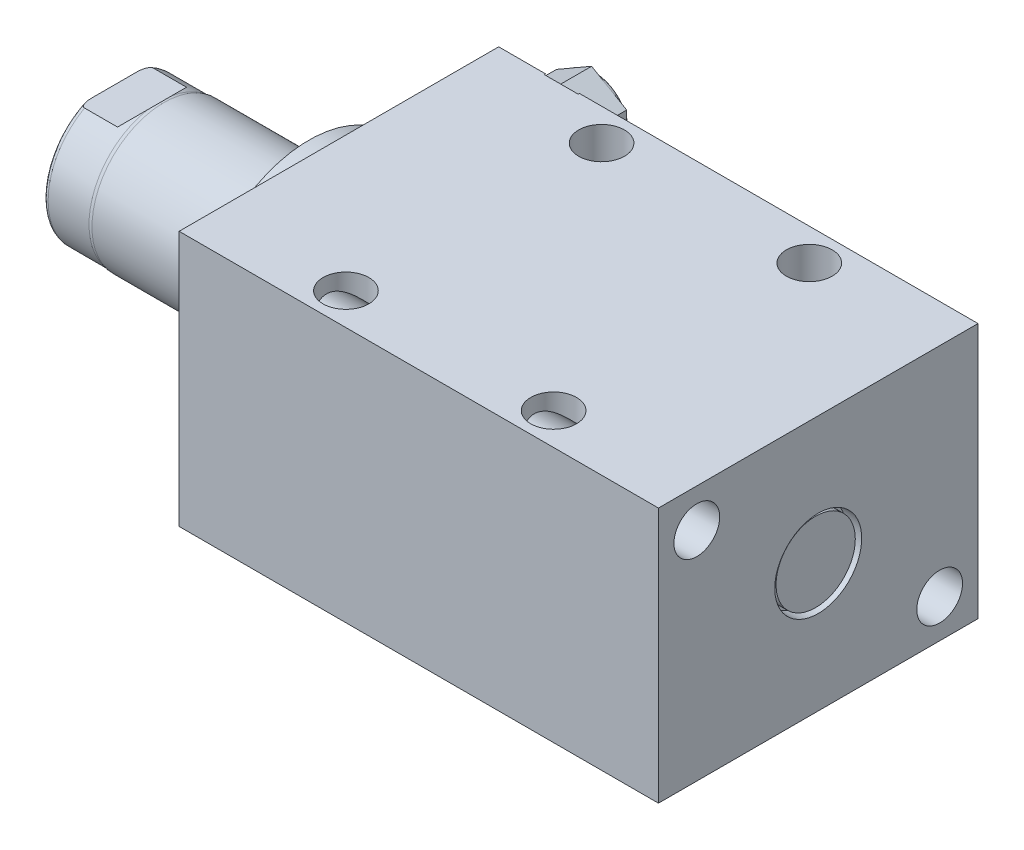
SolidWorks part; units mm, degrees
material "Alloy Steel"
ref_plane "Front Plane" through (0, 0, 0) normal (0, 0, 1) x (1, 0, 0)
ref_plane "Top Plane" through (0, 0, 0) normal (0, 1, 0) x (1, 0, 0)
ref_plane "Right Plane" through (0, 0, 0) normal (1, 0, 0) x (0, 0, -1)
ref_plane "Plane1" through (0, 0, 0) normal (1, 0, 0) x (0, 0, -1)
sketch "Sketch1" plane through (0, 0, 0) normal (1, 0, 0) x (0, 0, -1)
  line L0 (-31.75, 25.4) -> (31.75, 25.4)
  line L1 (31.75, 25.4) -> (31.75, -25.4)
  line L2 (31.75, -25.4) -> (-31.75, -25.4)
  line L3 (-31.75, -25.4) -> (-31.75, 25.4)
  line L4 (0, -24.4475) -> (0, 24.4475) construction
  dimension "D1" = 50.8
  dimension "D2" = 25.4
  dimension "D3" = 63.5
  dimension "D4" = 31.75
extrude "Extrude1" add sketch "Sketch1" along normal blind 95.25
ref_plane "Plane12" through (0, 17.45, 0) normal (0, 1, 0) x (-1, 0, 0)
sketch "S2D0002" plane through (0, 17.45, 0) normal (0, 1, 0) x (-1, 0, 0)
  line L0 (-17.7165, -31.496) -> (-21.336, -31.496)
  line L1 (-17.7165, -31.4706) -> (-17.7165, -31.496)
  line L2 (-17.7165, -31.4706) -> (-17.1196, -30.8737)
  line L3 (-17.1196, -30.8737) -> (-17.1196, -18.034)
  line L4 (-17.1196, -18.034) -> (-12.7, -18.034)
  line L5 (-12.7, -18.034) -> (-12.7, -31.75)
  line L6 (-12.7, -19.1384) -> (-12.7, 0.6985) construction
  line L7 (0, -31.75) -> (0, 31.75) construction
  line L8 (-21.336, -31.75) -> (-21.336, -31.496)
  line L9 (-95.25, -31.75) -> (0, -31.75) construction
  line L10 (-21.336, -31.75) -> (-12.7, -31.75)
  dimension "D1" = 13.716
  dimension "D2" = 12.7
  dimension "D3" = 8.8392
  dimension "D4" = 45
  dimension "D5" = 0.6223
  dimension "D6" = 10.033
  dimension "D7" = 0.0254
  dimension "D8" = 0.254
  dimension "D9" = 17.272
revolve "Cut-Revolve1" cut sketch "S2D0002" angle 360 about L6
pattern_linear "LPattern1" count 2 spacing 69.85 along (1, 0, 0) count 2 spacing 17.45 along (0, -1, 0) skipping (0, 1), (1, 0) of "Cut-Revolve1"
sketch "Sketch5" plane through (0, 0, 0) normal (-1, 0, 0) x (0, 0, 1)
  circle A0 centre (0, 0) radius 22.225
  dimension "D1" = 44.45
extrude "Extrude2" add sketch "Sketch5" along normal blind 5.969
ref_plane "Plane5" through (0, 0, 0) normal (0, -1, 0) x (0, 0, 1)
sketch "Sketch6" plane through (0, 0, 0) normal (0, -1, 0) x (0, 0, 1)
  line L0 (0, 5.969) -> (-14.2748, 5.969)
  line L1 (-14.2748, 5.969) -> (-14.2748, 44.704)
  line L2 (-14.2748, 44.704) -> (0, 44.704)
  line L3 (0, 44.704) -> (0, 5.969)
  line L4 (0, -5.7546) -> (0, 21.1709) construction
  line L5 (22.225, 5.969) -> (-22.225, 5.969) construction
  line L6 (31.75, -95.25) -> (-31.75, -95.25) construction
  dimension "D1" = 139.954
  dimension "D2" = 28.5496
revolve "Revolve1" add sketch "Sketch6" angle 360 about L4
ref_plane "Plane6" through (-18.5113, 3.2639, 0) normal (0, 0, 1) x (0, 1, 0)
sketch "S2D0001" plane through (-18.5113, 3.2639, 0) normal (0, 0, 1) x (0, 1, 0)
  line L0 (1.8671, 24.0814) -> (1.8671, 9.3527)
  line L1 (-3.2639, 9.3527) -> (1.8671, 9.3527)
  line L2 (3.0861, 26.1927) -> (-3.2639, 26.1927)
  line L3 (-3.2639, 26.1927) -> (-3.2639, 9.3527)
  line L4 (1.8671, 24.0814) -> (3.0861, 26.1927)
  line L5 (-3.2639, -18.5113) -> (-3.2639, 2.765) construction
  line L6 (11.0109, 26.1927) -> (-17.5387, 26.1927) construction
  dimension "D1" = 30
  dimension "D2" = 12.7
  dimension "D3" = 10.262
  dimension "D4" = 16.84
  dimension "D5" = 90
revolve "Cut-Revolve4" cut sketch "S2D0001" angle 360 about L5
ref_plane "Plane7" through (0, 0, 0) normal (0, 1, 0) x (0, 0, -1)
sketch "Sketch8" plane through (0, 0, 0) normal (0, 1, 0) x (0, 0, -1)
  line L0 (-14.2748, 34.798) -> (-14.097, 35.56)
  line L1 (-14.097, 35.56) -> (-14.097, 43.688)
  line L2 (0, 12.6594) -> (0, 20.8178) construction
  line L3 (-14.2748, 34.798) -> (-14.2748, 44.704)
  line L4 (-13.081, 44.704) -> (-14.2748, 44.704)
  line L5 (14.2748, 44.704) -> (-14.2748, 44.704) construction
  line L6 (-14.2748, 44.704) -> (-14.2748, 5.969) construction
  arc A0 (-13.081, 44.704) -> (-14.097, 43.688) centre (-13.081, 43.688) ccw
  dimension "D2" = 1.016
  dimension "D1" = 28.194
  dimension "D3" = 1.016
  dimension "D4" = 0.762
  dimension "D5" = 9.144
revolve "Cut-Revolve5" cut sketch "Sketch8" angle 360 about L2
ref_plane "Plane11" through (0, 0, 0) normal (0, 0, -1) x (0, -1, 0)
sketch "Sketch12" plane through (0, 0, 0) normal (0, 0, -1) x (0, -1, 0)
  line L0 (12.319, 44.704) -> (12.319, 37.135)
  line L1 (12.319, 37.135) -> (14.2748, 35.1792)
  line L2 (-12.319, 44.704) -> (-12.319, 37.135)
  line L3 (-12.319, 37.135) -> (-14.2748, 35.1792)
  line L4 (12.319, 44.704) -> (14.2748, 44.704)
  line L5 (0, 13.7262) -> (0, 20.767) construction
  line L6 (-14.2748, 35.1792) -> (-14.2748, 44.704)
  line L7 (14.2748, 5.969) -> (14.2748, 34.798) construction
  line L9 (14.2748, 35.1792) -> (14.2748, 44.704)
  line L10 (-12.319, 44.704) -> (-14.2748, 44.704)
  line L12 (13.081, 44.704) -> (-13.081, 44.704) construction
  dimension "D1" = 24.638
  dimension "D2" = 7.569
  dimension "D3" = 45
extrude "Cut-Extrude4" cut sketch "Sketch12" against normal mid plane 60.96
hole_wizard "Hole1" positions "Sketch15" profile "Sketch14" legacy end condition up to next
sketch "Sketch15" plane through (0, 0, 0) normal (-1, 0, 0) x (0, 0, 1)
  line L0 (0, 0) -> (-29.9914, 0) construction
  line L1 (0, 0) -> (0, 25.7648) construction
  point P0 (-24.13, -17.78)
  point P11 (24.13, 17.78)
  dimension "D1" = 17.78
  dimension "D2" = 24.13
  dimension "D3" = 35.56
  dimension "D4" = 48.26
sketch "Sketch14" plane through (0, -17.78, -24.13) normal (0, 1, 0) x (0, 0, 1)
  line L0 (0, 0) -> (0, 95.25)
  line L1 (0, 95.25) -> (4.5465, 95.25)
  line L2 (4.5465, 95.25) -> (4.5465, 0)
  line L3 (4.5465, 0) -> (0, 0)
  line L4 (0, 110) -> (0, -10) construction
  dimension "Diameter" = 9.093
  dimension "Depth" = 95.25
hole_wizard "Hole2" positions "Sketch17" profile "Sketch16" legacy
sketch "Sketch17" plane through (0, 25.4, 0) normal (0, 1, 0) x (-1, 0, 0)
  line L0 (0, 0) -> (-59.3363, 0) construction
  line L1 (0, -31.75) -> (0, 31.75) construction
  point P0 (-26.797, -25.4)
  point P9 (-26.797, 25.4)
  dimension "D1" = 50.8
  dimension "D2" = 26.797
  dimension "D3" = 25.4
sketch "Sketch16" plane through (26.797, 25.4, -25.4) normal (1, 0, 0) x (0, 0, 1)
  line L0 (0, 0) -> (0, 50.8)
  line L1 (0, 50.8) -> (4.5465, 50.8)
  line L2 (4.5465, 50.8) -> (4.5465, 0)
  line L3 (4.5465, 0) -> (0, 0)
  line L4 (0, 110) -> (0, -10) construction
  dimension "Diameter" = 9.093
  dimension "Depth" = 50.8
sketch "Sketch18" plane through (0, 0, -31.496) normal (0, 0, -1) x (-1, 0, 0)
  line L1 (-5.715, 21.4828) -> (-12.7, 25.5156)
  line L2 (-12.7, 25.5156) -> (-19.685, 21.4828)
  line L3 (-19.685, 21.4828) -> (-19.685, 13.4172)
  line L4 (-19.685, 13.4172) -> (-12.7, 9.3844)
  line L5 (-12.7, 9.3844) -> (-5.715, 13.4172)
  line L6 (-5.715, 13.4172) -> (-5.715, 21.4828)
  circle A0 centre (-12.7, 17.45) radius 6.985 construction
  dimension "D1" = 13.97
extrude "Extrude3" add sketch "Sketch18" along normal blind 6.78
sketch "Sketch19" plane through (0, 17.45, 0) normal (0, 1, 0) x (-1, 0, 0)
  line L0 (-12.7, -18.5103) -> (-12.7, -44.3941) construction
  line L1 (-12.7, -18.034) -> (-12.7, -30.8737) construction
  line L2 (-12.7, -38.276) -> (-19.685, -38.276) construction
  line L3 (-19.685, -38.276) -> (-19.685, -31.496) construction
  line L4 (-18.923, -38.276) -> (-18.923, -40.689)
  line L5 (-18.923, -40.689) -> (-22.098, -40.689)
  line L6 (-22.098, -40.689) -> (-22.098, -37.514)
  line L7 (-22.098, -37.514) -> (-19.685, -37.514)
  arc A0 (-19.685, -37.514) -> (-18.923, -38.276) centre (-18.923, -37.514) ccw
  dimension "D1" = 0.762
  dimension "D2" = 3.175
  dimension "D3" = 3.175
revolve "Cut-Revolve6" cut sketch "Sketch19" angle 360 about L0
sketch "Sketch20" plane through (0, 0, 0) normal (0, 1, 0) x (1, 0, 0)
  line L0 (0, 0) -> (70.5114, 0) construction
  line L1 (95.25, 8.636) -> (92.202, 8.636)
  line L2 (95.25, 31.75) -> (95.25, -31.75) construction
  line L3 (92.202, 8.636) -> (92.202, 5.0165)
  line L4 (92.202, 5.0165) -> (92.1766, 5.0165)
  line L5 (92.1766, 5.0165) -> (91.5797, 4.4196)
  line L6 (91.5797, 4.4196) -> (81.6356, 4.4196)
  line L7 (81.6356, 4.4196) -> (81.6356, 0)
  line L8 (81.6356, 0) -> (95.25, 0)
  line L9 (95.25, 0) -> (95.25, 8.636)
  dimension "D1" = 17.272
  dimension "D2" = 3.048
  dimension "D3" = 10.033
  dimension "D4" = 0.0254
  dimension "D5" = 45
  dimension "D6" = 8.8392
  dimension "D7" = 10.5664
revolve "Cut-Revolve7" cut sketch "Sketch20" angle 360 about L0
sketch "Sketch21" plane through (92.202, 0, 0) normal (1, 0, 0) x (0, 0, -1)
  circle A0 centre (0, 0) radius 7.874
  dimension "D1" = 15.748
extrude "Extrude4" add sketch "Sketch21" along normal blind 2.54
pattern_linear "LPattern2" count 2 spacing 41.275 along (1, 0, 0) of "Hole2"
